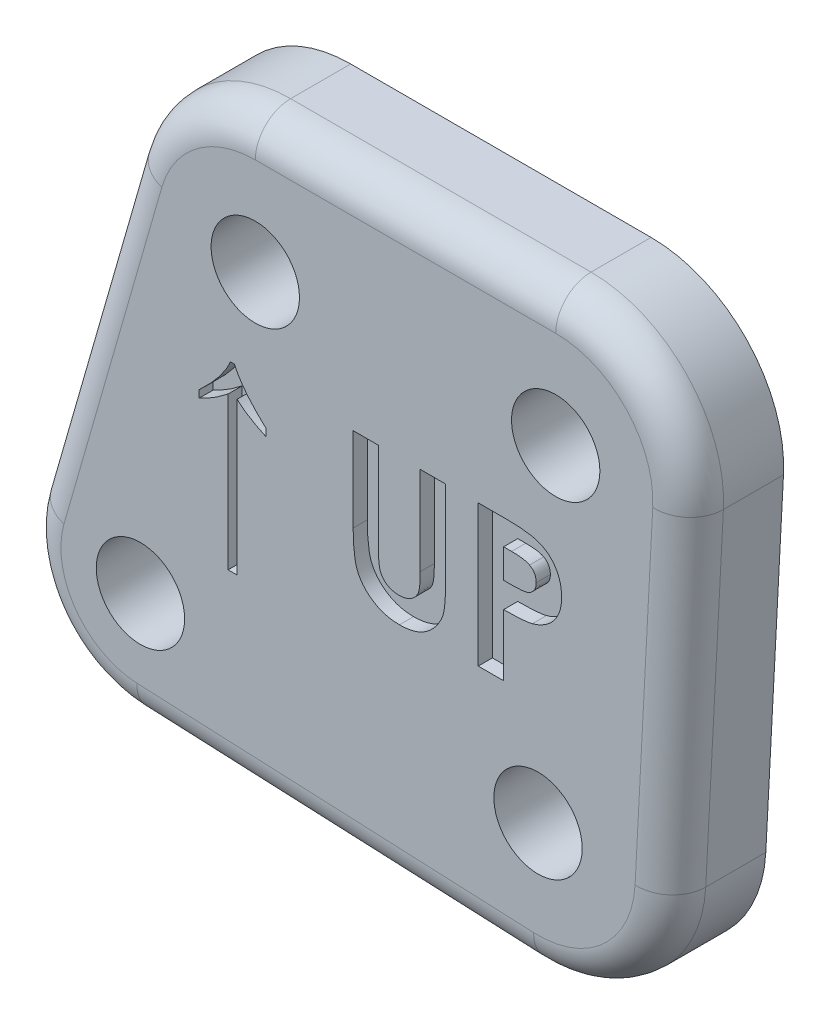
SolidWorks part; units mm, degrees
ref_plane "Front Plane" through (0, 0, 0) normal (0, 0, 1) x (1, 0, 0)
ref_plane "Top Plane" through (0, 0, 0) normal (0, 1, 0) x (1, 0, 0)
ref_plane "Right Plane" through (0, 0, 0) normal (1, 0, 0) x (0, 0, -1)
sketch "Sketch1" plane through (0, 0, 0) normal (0, 0, 1) x (1, 0, 0)
  line L0 (-4.5773, 1.3153) -> (-8.0945, -10.9251)
  line L1 (-4.3109, -16.1884) -> (9.9483, -16.8228)
  line L2 (14.9159, -12.3153) -> (15.5509, -0.2503)
  line L3 (10.795, 4.7625) -> (0, 4.7625)
  circle A0 centre (10.16, -12.065) radius 1.5875 construction
  circle A1 centre (10.795, 0) radius 1.5875 construction
  circle A2 centre (-4.1275, -12.065) radius 1.5875 construction
  circle A3 centre (0, 0) radius 1.5875 construction
  circle A4 centre (10.16, -12.065) radius 1.5875 construction
  circle A5 centre (10.795, 0) radius 1.5875 construction
  circle A6 centre (-4.1275, -12.065) radius 1.5875 construction
  circle A7 centre (0, 0) radius 1.5875 construction
  arc A8 (0, 4.7625) -> (-4.5773, 1.3153) centre (0, 0) ccw
  arc A9 (15.5509, -0.2503) -> (10.795, 4.7625) centre (10.795, 0) ccw
  arc A10 (9.9483, -16.8228) -> (14.9159, -12.3153) centre (10.16, -12.065) ccw
  arc A11 (-8.0945, -10.9251) -> (-4.3109, -16.1884) centre (-4.1275, -12.065) ccw
  circle A12 centre (-4.1275, -12.065) radius 4.1275 construction
  circle A13 centre (0, 0) radius 4.7625 construction
  circle A14 centre (10.795, 0) radius 4.7625 construction
  circle A15 centre (10.16, -12.065) radius 4.7625 construction
  dimension "D1" = 3.175
  dimension "D2" = 2.54
extrude "Boss-Extrude1" add sketch "Sketch1" against normal offset from surface (3.429 mm away) 0.127 contours L0 A11 L1 A10 L2 A9 L3 A8
hole_wizard "1/8 (0.1250) Dowel Hole1" positions "Sketch2" profile "Sketch3" hole size "1/8" standard "ANSI Inch" end condition through all
sketch "Sketch2" plane through (0, 0, 0) normal (0, 0, 1) x (1, 0, 0)
  point P0 (0, 0)
  point P3 (10.795, 0)
  point P6 (10.16, -12.065)
  point P9 (-4.1275, -12.065)
sketch "Sketch3" plane through (0, 0, 0) normal (1, 0, 0) x (0, -1, 0)
  line L0 (0, 0) -> (0, 3.429)
  line L1 (0, 3.429) -> (1.5875, 3.429)
  line L2 (1.5875, 3.429) -> (1.5875, 0)
  line L5 (1.5875, 0) -> (0, 0)
  line L11 (0, -6.35) -> (0, 107.95) construction
  dimension "Thru Hole Dia." = 3.175
  dimension "Thru Hole Depth" = 3.429
fillet "Fillet1" radius 1.27 8 edges at (-2.8651, 3.8043, 0) (5.3975, 4.7625, 0) (14.25, 3.2779, 0) (15.2334, -6.2828, 0) (13.3603, -15.592, 0) (2.8187, -16.5056, 0) (-7.4789, -14.4742, 0) (-6.3359, -4.8049, 0)
sketch "Sketch4" plane through (0, 0, 0) normal (0, 0, 1) x (1, 0, 0)
  line L0 (-2.54, -8.255) -> (8.5725, -8.255) construction
  line L1 (8.5725, -8.255) -> (8.5725, -12.065) construction
  line L2 (-2.54, -8.255) -> (-2.54, -12.065) construction
  line L3 (-4.1275, -16.1925) -> (10.16, -16.1925) construction
  circle A1 centre (-4.1275, -12.065) radius 1.5875 construction
  circle A3 centre (10.16, -12.065) radius 1.5875 construction
  text T0 "<b>↑ UP</b>" font "Century Gothic" height 5.08
  dimension "D1" = 3.81
  dimension "D2" = 13.6481
  dimension "D3" = 16.1925
extrude "Cut-Extrude1" cut sketch "Sketch4" against normal blind 0.508
